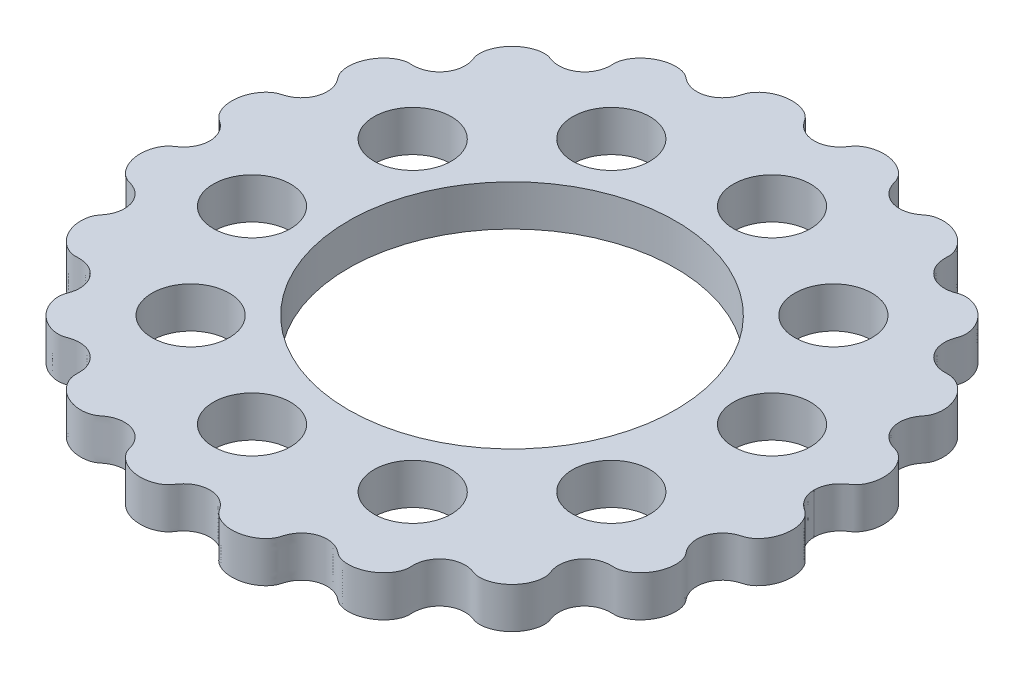
SolidWorks part; units mm, degrees
ref_plane "Front Plane" through (0, 0, 0) normal (0, 0, 1) x (1, 0, 0)
ref_plane "Top Plane" through (0, 0, 0) normal (0, 1, 0) x (1, 0, 0)
ref_plane "Right Plane" through (0, 0, 0) normal (1, 0, 0) x (0, 0, -1)
sketch "Sketch1" plane through (0, 0, 0) normal (0, 1, 0) x (1, 0, 0)
  line L0 (-115.1642, 0) -> (115.1642, 0) construction
  line L1 (0, 0) -> (71.6074, 11.3415)
  line L2 (0, 0) -> (49.3844, 7.8217)
  circle A0 centre (0, 0) radius 36
  circle A11 centre (49.3844, 7.8217) radius 8.5
  circle A12 centre (44.5503, -22.6995) radius 8.5
  circle A13 centre (22.6995, -44.5503) radius 8.5
  circle A14 centre (-7.8217, -49.3844) radius 8.5
  circle A15 centre (-35.3553, -35.3553) radius 8.5
  circle A16 centre (-49.3844, -7.8217) radius 8.5
  circle A17 centre (-44.5503, 22.6995) radius 8.5
  circle A18 centre (-22.6995, 44.5503) radius 8.5
  circle A19 centre (7.8217, 49.3844) radius 8.5
  circle A20 centre (35.3553, 35.3553) radius 8.5
  spline S0 degree 4 poles (65.4605, 29.5127) (65.4655, 29.1686) (65.4411, 28.6953) (65.3529, 28.0968) (65.1422, 27.3959) (64.9669, 26.9794) (64.7793, 26.6408) (64.5721, 26.3406) (64.3602, 26.0705) (64.1267, 25.7629) (63.886, 25.4071) (63.6576, 25.018) (63.4493, 24.5932) (63.2212, 24.0118) (63.0252, 23.2599) (62.9311, 22.3562) (63.0135, 21.3212) (63.2874, 20.3043) (63.7526, 19.3426) (64.4013, 18.4733) (65.1379, 17.8054) (65.8842, 17.3263) (66.5245, 17.0291) (66.9742, 16.8668) (67.3149, 16.7623) (67.5855, 16.6832) (67.8556, 16.6018) (68.139, 16.4927) (68.4292, 16.347) (68.7442, 16.1592) (69.1239, 15.8899) (69.5685, 15.5009) (70.0111, 15.0131) (70.4008, 14.4816) (70.6777, 14.0268) (70.8691, 13.6636) (70.9988, 13.3869) (71.0782, 13.2046) (71.1589, 13.0042) (71.23, 12.8148) (71.2726, 12.6939) (71.3209, 12.5457) (71.3774, 12.3645) (71.4665, 12.0546) (71.5573, 11.6609) (71.6461, 11.1378) (71.6973, 10.5855) (71.7141, 10.0755) (71.6934, 9.4422) (71.604, 8.684) (71.4252, 7.9197) (71.1461, 7.1625) (70.8392, 6.5565) (70.5425, 6.0894) (70.2317, 5.6994) (69.9193, 5.3829) (69.5974, 5.1276) (69.2839, 4.9185) (68.9179, 4.6631) (68.5115, 4.3444) (68.0178, 3.8822) (67.479, 3.228) (67.0049, 2.4212) (66.6487, 1.4477) (66.4722, 0.3979) (66.4959, -0.6726) (66.728, -1.7332) (67.1223, -2.6449) (67.6013, -3.3859) (68.0735, -3.9308) (68.4846, -4.3184) (68.8764, -4.6317) (69.2337, -4.8858) (69.5643, -5.1036) (69.8432, -5.3215) (70.1179, -5.5817) (70.4008, -5.9017) (70.7023, -6.3238) (71.0546, -6.9527) (71.3757, -7.7472) (71.6154, -8.6857) (71.7312, -9.759) (71.7014, -10.8232) (71.5361, -11.8601) (71.2442, -12.8535) (70.8335, -13.7883) (70.3588, -14.5657) (69.8607, -15.1916) (69.3853, -15.6662) (68.9647, -16.0122) (68.5481, -16.287) (68.1887, -16.4718) (67.8853, -16.5895) (67.6027, -16.679) (67.3177, -16.7605) (66.9147, -16.8851) (66.4027, -17.0799) (65.771, -17.3914) (65.047, -17.8802) (64.3539, -18.5333) (63.7378, -19.3727) (63.275, -20.3353) (63.0008, -21.3699) (62.9289, -22.4535) (63.0528, -23.4279) (63.2978, -24.2511) (63.587, -24.8932) (63.8609, -25.3718) (64.1452, -25.79) (64.4255, -26.1537) (64.7197, -26.5327) (64.9654, -26.9687) (65.1645, -27.4552) (65.3153, -27.9862) (65.4369, -28.6607) (65.4867, -29.4797) (65.4211, -30.426) (65.1959, -31.4778) (64.8335, -32.4836) (64.3459, -33.4278) (63.7436, -34.2955) (63.0364, -35.0719) (62.3194, -35.6676) (61.6326, -36.1029) (61.0186, -36.3975) (60.5014, -36.5851) (60.0027, -36.7056) (59.5828, -36.7546) (59.2387, -36.7552) (58.9195, -36.7455) (58.6002, -36.738) (58.1866, -36.7449) (57.6806, -36.7888) (57.0258, -36.9034) (56.2311, -37.1486) (55.3802, -37.5682) (54.5248, -38.2129) (53.7989, -39.0162) (53.2457, -39.9314) (52.8764, -40.9322) (52.7129, -41.9038) (52.7111, -42.801) (52.8153, -43.5274) (52.9414, -44.0332) (53.0556, -44.396) (53.1493, -44.6684) (53.2479, -44.939) (53.365, -45.2914) (53.4522, -45.7377) (53.492, -46.2577) (53.4686, -46.8459) (53.3634, -47.5564) (53.1367, -48.3745) (52.7684, -49.2465) (52.2349, -50.1437) (51.5838, -50.9705) (50.825, -51.7126) (49.9786, -52.3468) (49.0582, -52.8607) (48.2008, -53.1936) (47.4397, -53.384) (46.7836, -53.4712) (46.2434, -53.4905) (45.7356, -53.453) (45.3175, -53.3699) (44.9917, -53.2655) (44.6996, -53.161) (44.407, -53.0576) (44.0063, -52.933) (43.491, -52.8115) (42.8001, -52.7145) (41.9272, -52.71) (40.953, -52.8675) (39.9202, -53.2489) (38.9741, -53.8277) (38.1691, -54.5703) (37.5299, -55.4429) (37.1019, -56.344) (36.8793, -57.1248) (36.7803, -57.7595) (36.7454, -58.2289) (36.7381, -58.5957) (36.7456, -58.9543) (36.7588, -59.3048) (36.7453, -59.7001) (36.6779, -60.1352) (36.5493, -60.6146) (36.3491, -61.1297) (36.0405, -61.7408) (35.5897, -62.4233) (34.9769, -63.1346) (34.1812, -63.8335) (33.2956, -64.4242) (32.3354, -64.8968) (31.316, -65.2408) (30.2533, -65.4441) (29.3028, -65.4867) (28.4861, -65.415) (27.8172, -65.2736) (27.3586, -65.1269) (26.9828, -64.9645) (26.6415, -64.7795) (26.3825, -64.6044) (26.1435, -64.417) (25.8617, -64.202) (25.5735, -63.9954) (25.2136, -63.7661) (24.7736, -63.5314) (24.1733, -63.2738) (23.3906, -63.046) (22.4364, -62.9272) (21.3345, -63.0057) (20.2693, -63.297) (19.3028, -63.7777) (18.4651, -64.4155) (17.8212, -65.1237) (17.3489, -65.8446) (17.0492, -66.4737) (16.8796, -66.9362) (16.7731, -67.2787) (16.697, -67.538) (16.6206, -67.7971) (16.4999, -68.13) (16.3026, -68.5209) (16.0236, -68.9517) (15.6499, -69.4069) (15.1392, -69.9099) (14.4692, -70.4259) (13.6607, -70.8988) (12.7127, -71.2944) (11.702, -71.5708) (10.6433, -71.7174) (9.5744, -71.7223) (8.5152, -71.5812) (7.6197, -71.3301) (6.8918, -71.0218) (6.3681, -70.7238) (6.0257, -70.4887) (5.7564, -70.2722) (5.5526, -70.086) (5.3293, -69.8531) (5.1014, -69.5624) (4.8738, -69.215) (4.6046, -68.8398) (4.2946, -68.4584) (3.9347, -68.0813) (3.4174, -67.6285) (2.7042, -67.1529) (1.7921, -66.7433) (0.6851, -66.4941) (-0.4667, -66.4704) (-1.4606, -66.6552) (-2.2728, -66.9558) (-2.9107, -67.2974) (-3.3788, -67.6111) (-3.7983, -67.9554) (-4.1704, -68.3213) (-4.4603, -68.6577) (-4.6823, -68.9486) (-4.8581, -69.1976) (-4.9952, -69.3993) (-5.1396, -69.6076) (-5.3007, -69.8157) (-5.4839, -70.0179) (-5.6881, -70.2127) (-5.9591, -70.4393) (-6.3053, -70.6848) (-6.8327, -70.9933) (-7.5648, -71.3113) (-8.469, -71.5723) (-9.5418, -71.7212) (-10.6244, -71.7198) (-11.6959, -71.5725) (-12.7127, -71.2944) (-13.6607, -70.8988) (-14.4692, -70.4259) (-15.1392, -69.9099) (-15.6499, -69.4069) (-16.0236, -68.9517) (-16.3026, -68.5209) (-16.4999, -68.13) (-16.6206, -67.7971) (-16.697, -67.538) (-16.7731, -67.2787) (-16.8796, -66.9362) (-17.0492, -66.4737) (-17.3489, -65.8446) (-17.8212, -65.1237) (-18.4651, -64.4155) (-19.3028, -63.7777) (-20.2693, -63.297) (-21.3345, -63.0057) (-22.4364, -62.9272) (-23.3906, -63.046) (-24.1733, -63.2738) (-24.7736, -63.5314) (-25.2137, -63.7661) (-25.5735, -63.9954) (-25.8617, -64.202) (-26.0964, -64.3813) (-26.2831, -64.5262) (-26.4805, -64.6709) (-26.6936, -64.8076) (-26.9828, -64.9646) (-27.3587, -65.1269) (-27.8172, -65.2736) (-28.4861, -65.415) (-29.3028, -65.4868) (-30.2533, -65.4441) (-31.316, -65.2408) (-32.3354, -64.8968) (-33.2956, -64.4242) (-34.1812, -63.8335) (-34.9769, -63.1346) (-35.5897, -62.4233) (-36.0405, -61.7408) (-36.3491, -61.1297) (-36.5493, -60.6146) (-36.6779, -60.1352) (-36.7453, -59.7001) (-36.7588, -59.3048) (-36.7456, -58.9543) (-36.7381, -58.5957) (-36.7454, -58.2289) (-36.7803, -57.7595) (-36.8793, -57.1248) (-37.1019, -56.344) (-37.5299, -55.4429) (-38.1691, -54.5703) (-38.9741, -53.8277) (-39.9202, -53.2489) (-40.953, -52.8675) (-41.9272, -52.71) (-42.8001, -52.7145) (-43.491, -52.8115) (-44.0063, -52.933) (-44.407, -53.0576) (-44.6996, -53.161) (-44.9917, -53.2655) (-45.3175, -53.3699) (-45.7356, -53.453) (-46.2434, -53.4905) (-46.7836, -53.4712) (-47.4397, -53.384) (-48.2008, -53.1936) (-49.0582, -52.8607) (-49.9786, -52.3468) (-50.825, -51.7126) (-51.5838, -50.9705) (-52.2349, -50.1437) (-52.7684, -49.2465) (-53.1367, -48.3745) (-53.3634, -47.5564) (-53.4686, -46.8459) (-53.492, -46.2577) (-53.4522, -45.7377) (-53.365, -45.2914) (-53.2479, -44.939) (-53.1493, -44.6684) (-53.0556, -44.396) (-52.9697, -44.1229) (-52.8837, -43.8018) (-52.7883, -43.3387) (-52.7113, -42.7066) (-52.7129, -41.9038) (-52.8764, -40.9322) (-53.2457, -39.9314) (-53.7989, -39.0162) (-54.5248, -38.2129) (-55.3802, -37.5682) (-56.2311, -37.1486) (-57.0258, -36.9034) (-57.6806, -36.7888) (-58.1866, -36.7449) (-58.6002, -36.738) (-58.9195, -36.7455) (-59.2387, -36.7552) (-59.5828, -36.7546) (-60.0027, -36.7056) (-60.5014, -36.5851) (-61.0186, -36.3975) (-61.6326, -36.1029) (-62.3194, -35.6676) (-63.0364, -35.0719) (-63.7436, -34.2955) (-64.3459, -33.4278) (-64.8335, -32.4836) (-65.1959, -31.4778) (-65.4211, -30.426) (-65.4867, -29.4797) (-65.4369, -28.6607) (-65.3153, -27.9862) (-65.1645, -27.4552) (-64.9654, -26.9687) (-64.7197, -26.5327) (-64.4255, -26.1537) (-64.1452, -25.79) (-63.8609, -25.3718) (-63.587, -24.8932) (-63.2978, -24.2511) (-63.0528, -23.4279) (-62.9289, -22.4535) (-63.0008, -21.3699) (-63.275, -20.3353) (-63.7378, -19.3727) (-64.3539, -18.5333) (-65.047, -17.8802) (-65.771, -17.3914) (-66.4027, -17.0799) (-66.9147, -16.8851) (-67.3177, -16.7605) (-67.6027, -16.679) (-67.8853, -16.5895) (-68.1887, -16.4718) (-68.5481, -16.287) (-68.9647, -16.0122) (-69.3853, -15.6662) (-69.8607, -15.1916) (-70.3588, -14.5657) (-70.8335, -13.7883) (-71.2442, -12.8535) (-71.5361, -11.8601) (-71.7014, -10.8232) (-71.7312, -9.759) (-71.6154, -8.6857) (-71.3757, -7.7472) (-71.0546, -6.9527) (-70.7023, -6.3238) (-70.4008, -5.9017) (-70.1179, -5.5817) (-69.8432, -5.3215) (-69.5643, -5.1036) (-69.2337, -4.8858) (-68.8764, -4.6317) (-68.4846, -4.3184) (-68.0735, -3.9308) (-67.6013, -3.3859) (-67.1223, -2.6449) (-66.728, -1.7332) (-66.4959, -0.6726) (-66.4722, 0.3979) (-66.6487, 1.4477) (-67.0049, 2.4212) (-67.479, 3.228) (-68.0178, 3.8822) (-68.5115, 4.3445) (-68.9179, 4.6631) (-69.2839, 4.9185) (-69.5974, 5.1275) (-69.9193, 5.3829) (-70.2317, 5.6994) (-70.5425, 6.0895) (-70.8393, 6.5564) (-71.1461, 7.1627) (-71.4254, 7.9193) (-71.6038, 8.6846) (-71.6937, 9.4414) (-71.7137, 10.0768) (-71.6982, 10.5829) (-71.6528, 11.0541) (-71.5898, 11.476) (-71.5079, 11.8717) (-71.4425, 12.139) (-71.3774, 12.3645) (-71.3208, 12.546) (-71.2727, 12.6938) (-71.23, 12.8149) (-71.1589, 13.0042) (-71.0782, 13.2046) (-70.9988, 13.3869) (-70.8691, 13.6636) (-70.6777, 14.0268) (-70.4008, 14.4816) (-70.0111, 15.0131) (-69.5685, 15.5009) (-69.1239, 15.8899) (-68.7442, 16.1592) (-68.4292, 16.347) (-68.139, 16.4927) (-67.8556, 16.6018) (-67.5855, 16.6832) (-67.3149, 16.7623) (-66.9742, 16.8668) (-66.5245, 17.0291) (-65.8842, 17.3263) (-65.1379, 17.8054) (-64.4013, 18.4733) (-63.7491, 19.3473) (-63.28, 20.3205) (-63.0059, 21.3554) (-62.9309, 22.4063) (-63.0352, 23.3171) (-63.2396, 24.0678) (-63.4711, 24.642) (-63.6812, 25.0611) (-63.9101, 25.4449) (-64.1204, 25.7515) (-64.3116, 26.0062) (-64.4807, 26.2243) (-64.6214, 26.4108) (-64.7943, 26.6657) (-64.9775, 27.0024) (-65.1491, 27.4157) (-65.3551, 28.1105) (-65.4416, 28.7032) (-65.4654, 29.172) (-65.4605, 29.5127) knots 0 0 0 0 0 0.004123 0.005669 0.007215 0.008756 0.009527 0.010298 0.011583 0.012869 0.014155 0.015441 0.016987 0.018533 0.02163 0.024723 0.027815 0.030907 0.034179 0.03745 0.040732 0.042749 0.044767 0.045893 0.046456 0.04702 0.048146 0.049273 0.050089 0.050906 0.052538 0.054845 0.057151 0.058784 0.060416 0.061233 0.062049 0.062457 0.062865 0.063682 0.064216 0.064483 0.06475 0.065818 0.067955 0.069475 0.070996 0.072517 0.074037 0.077079 0.08012 0.0819 0.08368 0.085209 0.086738 0.087867 0.088995 0.090124 0.091252 0.093215 0.095179 0.098214 0.101374 0.104369 0.107533 0.1109 0.114125 0.117298 0.119365 0.121433 0.122746 0.124059 0.125372 0.126686 0.12749 0.128294 0.129902 0.131797 0.133692 0.136915 0.140139 0.143363 0.146587 0.149637 0.152687 0.155738 0.158788 0.160518 0.162248 0.163776 0.165304 0.166488 0.16708 0.167672 0.168855 0.170039 0.172134 0.174229 0.177278 0.18047 0.183483 0.186637 0.190007 0.193215 0.196415 0.198338 0.200262 0.201638 0.203015 0.204391 0.205768 0.207378 0.208989 0.210679 0.212369 0.215581 0.218794 0.222006 0.225218 0.228355 0.231492 0.234629 0.237765 0.239488 0.24121 0.242778 0.244347 0.245622 0.24626 0.246898 0.248174 0.24945 0.251214 0.252979 0.256128 0.259382 0.262517 0.265738 0.269027 0.272117 0.275225 0.277481 0.279736 0.280887 0.281463 0.282038 0.283189 0.28434 0.285906 0.287472 0.289426 0.29138 0.294497 0.297615 0.300733 0.30385 0.307074 0.310298 0.313371 0.316443 0.31806 0.319676 0.321293 0.322909 0.324149 0.324768 0.325388 0.326627 0.327867 0.329796 0.331725 0.334972 0.338289 0.341548 0.344836 0.34818 0.35133 0.354431 0.356724 0.35787 0.359017 0.360068 0.361118 0.362169 0.36322 0.3648 0.366381 0.368106 0.36983 0.372993 0.376156 0.379319 0.382483 0.385713 0.388944 0.392175 0.395406 0.397073 0.39874 0.400356 0.401164 0.401972 0.403388 0.404096 0.404804 0.40622 0.407635 0.409205 0.410774 0.414037 0.417372 0.420655 0.423928 0.427187 0.430227 0.4332 0.43534 0.437479 0.438558 0.439098 0.439638 0.440717 0.441796 0.443334 0.444872 0.446856 0.44884 0.451909 0.454977 0.458046 0.461115 0.464432 0.467749 0.470814 0.47388 0.475539 0.477198 0.478024 0.478851 0.479677 0.480504 0.481887 0.48327 0.484653 0.486036 0.487772 0.489508 0.492878 0.49627 0.499675 0.503014 0.506592 0.508301 0.51001 0.511672 0.513334 0.514795 0.516256 0.516987 0.517718 0.518448 0.519179 0.520024 0.520869 0.521714 0.522559 0.524254 0.525949 0.529024 0.532099 0.535492 0.538885 0.541954 0.545023 0.548091 0.55116 0.553144 0.555128 0.556666 0.558204 0.559283 0.560362 0.560902 0.561442 0.562521 0.56466 0.5668 0.569773 0.572812 0.576072 0.579345 0.582628 0.585963 0.589226 0.590795 0.592365 0.59378 0.595196 0.595904 0.596612 0.59732 0.598028 0.598836 0.599644 0.60126 0.602927 0.604594 0.607825 0.611056 0.614287 0.617517 0.620681 0.623844 0.627007 0.63017 0.631894 0.633619 0.635199 0.63678 0.637831 0.638882 0.639932 0.640983 0.64213 0.643276 0.645569 0.64867 0.65182 0.655164 0.658452 0.661711 0.665028 0.668275 0.670204 0.672133 0.673372 0.674612 0.675232 0.675851 0.677091 0.678707 0.680324 0.68194 0.683557 0.686629 0.689702 0.692926 0.69615 0.699267 0.702385 0.705503 0.70862 0.710574 0.712528 0.714094 0.71566 0.716811 0.717962 0.718537 0.719113 0.720264 0.721391 0.722519 0.724775 0.727883 0.730973 0.734262 0.737483 0.740618 0.743872 0.747021 0.748786 0.75055 0.751826 0.753102 0.75374 0.754378 0.755653 0.757222 0.75879 0.760512 0.762234 0.765371 0.768508 0.771645 0.774782 0.777994 0.781206 0.784419 0.787631 0.789321 0.791011 0.792622 0.794232 0.795609 0.796985 0.798362 0.799738 0.801662 0.803585 0.806785 0.809993 0.813363 0.816517 0.81953 0.822722 0.825771 0.827866 0.829961 0.831145 0.832328 0.83292 0.833512 0.834696 0.836224 0.837752 0.839482 0.841212 0.844262 0.847313 0.850363 0.853413 0.856637 0.859861 0.863084 0.866308 0.868203 0.870098 0.871706 0.87251 0.873314 0.874628 0.875941 0.877254 0.878567 0.880635 0.882702 0.885875 0.8891 0.892467 0.895631 0.898626 0.901786 0.904821 0.906785 0.908748 0.909876 0.911005 0.912133 0.913262 0.914791 0.91632 0.9181 0.91988 0.922921 0.925963 0.927483 0.929004 0.930525 0.932045 0.933114 0.934182 0.93525 0.935517 0.935784 0.936318 0.937135 0.937543 0.937951 0.938767 0.939584 0.941216 0.942849 0.945155 0.947462 0.949094 0.949911 0.950727 0.951854 0.95298 0.953544 0.954107 0.955233 0.957251 0.959268 0.96255 0.965821 0.969093 0.972255 0.975418 0.978575 0.981646 0.98318 0.984714 0.985986 0.987258 0.98853 0.989166 0.989802 0.990566 0.991329 0.992855 0.994386 0.995917 1 1 1 1 1 construction
  spline S1 degree 4 poles (66.5, 0) (66.5, -0.3064) (66.5419, -0.882) (66.7179, -1.7097) (67.1223, -2.6449) (67.6013, -3.3859) (68.0735, -3.9308) (68.4846, -4.3184) (68.8764, -4.6317) (69.2337, -4.8858) (69.5643, -5.1036) (69.8432, -5.3215) (70.1179, -5.5817) (70.4008, -5.9017) (70.7023, -6.3238) (71.0546, -6.9527) (71.3757, -7.7472) (71.6154, -8.6857) (71.7312, -9.759) (71.7014, -10.8232) (71.5361, -11.8601) (71.2442, -12.8535) (70.8335, -13.7883) (70.3588, -14.5657) (69.8607, -15.1916) (69.3853, -15.6662) (68.9647, -16.0122) (68.5481, -16.287) (68.1887, -16.4718) (67.8853, -16.5895) (67.6027, -16.679) (67.3177, -16.7605) (66.9147, -16.8851) (66.4027, -17.0799) (65.771, -17.3914) (65.047, -17.8802) (64.3539, -18.5333) (63.7378, -19.3727) (63.275, -20.3353) (63.0008, -21.3699) (62.9289, -22.4535) (63.0528, -23.4279) (63.2978, -24.2511) (63.587, -24.8932) (63.8609, -25.3718) (64.1452, -25.79) (64.4255, -26.1537) (64.7197, -26.5327) (64.9654, -26.9687) (65.1645, -27.4552) (65.3153, -27.9862) (65.4369, -28.6607) (65.4867, -29.4797) (65.4211, -30.426) (65.1959, -31.4778) (64.8335, -32.4836) (64.3459, -33.4278) (63.7436, -34.2955) (63.0364, -35.0719) (62.3194, -35.6676) (61.6326, -36.1029) (61.0186, -36.3975) (60.5014, -36.5851) (60.0027, -36.7056) (59.5828, -36.7546) (59.2387, -36.7552) (58.9195, -36.7455) (58.6002, -36.738) (58.1866, -36.7449) (57.6806, -36.7888) (57.0258, -36.9034) (56.2311, -37.1486) (55.3802, -37.5682) (54.5248, -38.2129) (53.7989, -39.0162) (53.2457, -39.9314) (52.8764, -40.9322) (52.7129, -41.9038) (52.7111, -42.801) (52.8153, -43.5274) (52.9414, -44.0332) (53.0556, -44.396) (53.1493, -44.6684) (53.2479, -44.939) (53.365, -45.2914) (53.4522, -45.7377) (53.492, -46.2577) (53.4686, -46.8459) (53.3634, -47.5564) (53.1367, -48.3745) (52.7684, -49.2465) (52.2349, -50.1437) (51.5838, -50.9705) (50.825, -51.7126) (49.9786, -52.3468) (49.0582, -52.8607) (48.2008, -53.1936) (47.4397, -53.384) (46.7836, -53.4712) (46.2434, -53.4905) (45.7356, -53.453) (45.3175, -53.3699) (44.9917, -53.2655) (44.6996, -53.161) (44.407, -53.0576) (44.0063, -52.933) (43.491, -52.8115) (42.8001, -52.7145) (41.9272, -52.71) (40.953, -52.8675) (39.9202, -53.2489) (38.9741, -53.8277) (38.1691, -54.5703) (37.5299, -55.4429) (37.1019, -56.344) (36.8793, -57.1248) (36.7803, -57.7595) (36.7454, -58.2289) (36.7381, -58.5957) (36.7456, -58.9543) (36.7588, -59.3048) (36.7453, -59.7001) (36.6779, -60.1352) (36.5493, -60.6146) (36.3491, -61.1297) (36.0405, -61.7408) (35.5897, -62.4233) (34.9769, -63.1346) (34.1812, -63.8335) (33.2956, -64.4242) (32.3354, -64.8968) (31.316, -65.2408) (30.2533, -65.4441) (29.3028, -65.4867) (28.4861, -65.415) (27.8172, -65.2736) (27.3586, -65.1269) (26.9828, -64.9645) (26.6415, -64.7795) (26.3825, -64.6044) (26.1435, -64.417) (25.8617, -64.202) (25.5735, -63.9954) (25.2136, -63.7661) (24.7736, -63.5314) (24.1733, -63.2738) (23.3906, -63.046) (22.4364, -62.9272) (21.3345, -63.0057) (20.2693, -63.297) (19.3028, -63.7777) (18.4651, -64.4155) (17.8212, -65.1237) (17.3489, -65.8446) (17.0492, -66.4737) (16.8796, -66.9362) (16.7731, -67.2787) (16.697, -67.538) (16.6206, -67.7971) (16.4999, -68.13) (16.3026, -68.5209) (16.0236, -68.9517) (15.6499, -69.4069) (15.1392, -69.9099) (14.4692, -70.4259) (13.6607, -70.8988) (12.7127, -71.2944) (11.702, -71.5708) (10.6433, -71.7174) (9.5744, -71.7223) (8.5152, -71.5812) (7.6197, -71.3301) (6.8918, -71.0218) (6.3681, -70.7238) (6.0257, -70.4887) (5.7564, -70.2722) (5.5526, -70.086) (5.3293, -69.8531) (5.1014, -69.5624) (4.8738, -69.215) (4.6046, -68.8398) (4.2946, -68.4584) (3.9347, -68.0813) (3.4174, -67.6285) (2.7042, -67.1529) (1.7921, -66.7433) (0.6851, -66.4941) (-0.4667, -66.4704) (-1.4606, -66.6552) (-2.2728, -66.9558) (-2.9107, -67.2974) (-3.3788, -67.6111) (-3.7983, -67.9554) (-4.1704, -68.3213) (-4.4603, -68.6577) (-4.6823, -68.9486) (-4.8581, -69.1976) (-4.9952, -69.3993) (-5.1396, -69.6076) (-5.3007, -69.8157) (-5.4839, -70.0179) (-5.6881, -70.2127) (-5.9591, -70.4393) (-6.3053, -70.6848) (-6.8327, -70.9933) (-7.5648, -71.3113) (-8.469, -71.5723) (-9.5418, -71.7212) (-10.6244, -71.7198) (-11.6959, -71.5725) (-12.7127, -71.2944) (-13.6607, -70.8988) (-14.4692, -70.4259) (-15.1392, -69.9099) (-15.6499, -69.4069) (-16.0236, -68.9517) (-16.3026, -68.5209) (-16.4999, -68.13) (-16.6206, -67.7971) (-16.697, -67.538) (-16.7731, -67.2787) (-16.8796, -66.9362) (-17.0492, -66.4737) (-17.3489, -65.8446) (-17.8212, -65.1237) (-18.4651, -64.4155) (-19.3028, -63.7777) (-20.2693, -63.297) (-21.3345, -63.0057) (-22.4364, -62.9272) (-23.3906, -63.046) (-24.1733, -63.2738) (-24.7736, -63.5314) (-25.2137, -63.7661) (-25.5735, -63.9954) (-25.8617, -64.202) (-26.0964, -64.3813) (-26.2831, -64.5262) (-26.4805, -64.6709) (-26.6936, -64.8076) (-26.9828, -64.9646) (-27.3587, -65.1269) (-27.8172, -65.2736) (-28.4861, -65.415) (-29.3028, -65.4868) (-30.2533, -65.4441) (-31.316, -65.2408) (-32.3354, -64.8968) (-33.2956, -64.4242) (-34.1812, -63.8335) (-34.9769, -63.1346) (-35.5897, -62.4233) (-36.0405, -61.7408) (-36.3491, -61.1297) (-36.5493, -60.6146) (-36.6779, -60.1352) (-36.7453, -59.7001) (-36.7588, -59.3048) (-36.7456, -58.9543) (-36.7381, -58.5957) (-36.7454, -58.2289) (-36.7803, -57.7595) (-36.8793, -57.1248) (-37.1019, -56.344) (-37.5299, -55.4429) (-38.1691, -54.5703) (-38.9741, -53.8277) (-39.9202, -53.2489) (-40.953, -52.8675) (-41.9272, -52.71) (-42.8001, -52.7145) (-43.491, -52.8115) (-44.0063, -52.933) (-44.407, -53.0576) (-44.6996, -53.161) (-44.9917, -53.2655) (-45.3175, -53.3699) (-45.7356, -53.453) (-46.2434, -53.4905) (-46.7836, -53.4712) (-47.4397, -53.384) (-48.2008, -53.1936) (-49.0582, -52.8607) (-49.9786, -52.3468) (-50.825, -51.7126) (-51.5838, -50.9705) (-52.2349, -50.1437) (-52.7684, -49.2465) (-53.1367, -48.3745) (-53.3634, -47.5564) (-53.4686, -46.8459) (-53.492, -46.2577) (-53.4522, -45.7377) (-53.365, -45.2914) (-53.2479, -44.939) (-53.1493, -44.6684) (-53.0556, -44.396) (-52.9697, -44.1229) (-52.8837, -43.8018) (-52.7883, -43.3387) (-52.7113, -42.7066) (-52.7129, -41.9038) (-52.8764, -40.9322) (-53.2457, -39.9314) (-53.7989, -39.0162) (-54.5248, -38.2129) (-55.3802, -37.5682) (-56.2311, -37.1486) (-57.0258, -36.9034) (-57.6806, -36.7888) (-58.1866, -36.7449) (-58.6002, -36.738) (-58.9195, -36.7455) (-59.2387, -36.7552) (-59.5828, -36.7546) (-60.0027, -36.7056) (-60.5014, -36.5851) (-61.0186, -36.3975) (-61.6326, -36.1029) (-62.3194, -35.6676) (-63.0364, -35.0719) (-63.7436, -34.2955) (-64.3459, -33.4278) (-64.8335, -32.4836) (-65.1959, -31.4778) (-65.4211, -30.426) (-65.4867, -29.4797) (-65.4369, -28.6607) (-65.3153, -27.9862) (-65.1645, -27.4552) (-64.9654, -26.9687) (-64.7197, -26.5327) (-64.4255, -26.1537) (-64.1452, -25.79) (-63.8609, -25.3718) (-63.587, -24.8932) (-63.2978, -24.2511) (-63.0528, -23.4279) (-62.9289, -22.4535) (-63.0008, -21.3699) (-63.275, -20.3353) (-63.7378, -19.3727) (-64.3539, -18.5333) (-65.047, -17.8802) (-65.771, -17.3914) (-66.4027, -17.0799) (-66.9147, -16.8851) (-67.3177, -16.7605) (-67.6027, -16.679) (-67.8853, -16.5895) (-68.1887, -16.4718) (-68.5481, -16.287) (-68.9647, -16.0122) (-69.3853, -15.6662) (-69.8607, -15.1916) (-70.3588, -14.5657) (-70.8335, -13.7883) (-71.2442, -12.8535) (-71.5361, -11.8601) (-71.7014, -10.8232) (-71.7312, -9.759) (-71.6154, -8.6857) (-71.3757, -7.7472) (-71.0546, -6.9527) (-70.7023, -6.3238) (-70.4008, -5.9017) (-70.1179, -5.5817) (-69.8432, -5.3215) (-69.5643, -5.1036) (-69.2337, -4.8858) (-68.8764, -4.6317) (-68.4846, -4.3184) (-68.0735, -3.9308) (-67.6013, -3.3859) (-67.1223, -2.6449) (-66.7179, -1.7097) (-66.5419, -0.882) (-66.5, -0.3064) (-66.5, 0) knots 0.107228 0.107228 0.107228 0.107228 0.107228 0.1109 0.114125 0.117298 0.119365 0.121433 0.122746 0.124059 0.125372 0.126686 0.12749 0.128294 0.129902 0.131797 0.133692 0.136915 0.140139 0.143363 0.146587 0.149637 0.152687 0.155738 0.158788 0.160518 0.162248 0.163776 0.165304 0.166488 0.16708 0.167672 0.168855 0.170039 0.172134 0.174229 0.177278 0.18047 0.183483 0.186637 0.190007 0.193215 0.196415 0.198338 0.200262 0.201638 0.203015 0.204391 0.205768 0.207378 0.208989 0.210679 0.212369 0.215581 0.218794 0.222006 0.225218 0.228355 0.231492 0.234629 0.237765 0.239488 0.24121 0.242778 0.244347 0.245622 0.24626 0.246898 0.248174 0.24945 0.251214 0.252979 0.256128 0.259382 0.262517 0.265738 0.269027 0.272117 0.275225 0.277481 0.279736 0.280887 0.281463 0.282038 0.283189 0.28434 0.285906 0.287472 0.289426 0.29138 0.294497 0.297615 0.300733 0.30385 0.307074 0.310298 0.313371 0.316443 0.31806 0.319676 0.321293 0.322909 0.324149 0.324768 0.325388 0.326627 0.327867 0.329796 0.331725 0.334972 0.338289 0.341548 0.344836 0.34818 0.35133 0.354431 0.356724 0.35787 0.359017 0.360068 0.361118 0.362169 0.36322 0.3648 0.366381 0.368106 0.36983 0.372993 0.376156 0.379319 0.382483 0.385713 0.388944 0.392175 0.395406 0.397073 0.39874 0.400356 0.401164 0.401972 0.403388 0.404096 0.404804 0.40622 0.407635 0.409205 0.410774 0.414037 0.417372 0.420655 0.423928 0.427187 0.430227 0.4332 0.43534 0.437479 0.438558 0.439098 0.439638 0.440717 0.441796 0.443334 0.444872 0.446856 0.44884 0.451909 0.454977 0.458046 0.461115 0.464432 0.467749 0.470814 0.47388 0.475539 0.477198 0.478024 0.478851 0.479677 0.480504 0.481887 0.48327 0.484653 0.486036 0.487772 0.489508 0.492878 0.49627 0.499675 0.503014 0.506592 0.508301 0.51001 0.511672 0.513334 0.514795 0.516256 0.516987 0.517718 0.518448 0.519179 0.520024 0.520869 0.521714 0.522559 0.524254 0.525949 0.529024 0.532099 0.535492 0.538885 0.541954 0.545023 0.548091 0.55116 0.553144 0.555128 0.556666 0.558204 0.559283 0.560362 0.560902 0.561442 0.562521 0.56466 0.5668 0.569773 0.572812 0.576072 0.579345 0.582628 0.585963 0.589226 0.590795 0.592365 0.59378 0.595196 0.595904 0.596612 0.59732 0.598028 0.598836 0.599644 0.60126 0.602927 0.604594 0.607825 0.611056 0.614287 0.617517 0.620681 0.623844 0.627007 0.63017 0.631894 0.633619 0.635199 0.63678 0.637831 0.638882 0.639932 0.640983 0.64213 0.643276 0.645569 0.64867 0.65182 0.655164 0.658452 0.661711 0.665028 0.668275 0.670204 0.672133 0.673372 0.674612 0.675232 0.675851 0.677091 0.678707 0.680324 0.68194 0.683557 0.686629 0.689702 0.692926 0.69615 0.699267 0.702385 0.705503 0.70862 0.710574 0.712528 0.714094 0.71566 0.716811 0.717962 0.718537 0.719113 0.720264 0.721391 0.722519 0.724775 0.727883 0.730973 0.734262 0.737483 0.740618 0.743872 0.747021 0.748786 0.75055 0.751826 0.753102 0.75374 0.754378 0.755653 0.757222 0.75879 0.760512 0.762234 0.765371 0.768508 0.771645 0.774782 0.777994 0.781206 0.784419 0.787631 0.789321 0.791011 0.792622 0.794232 0.795609 0.796985 0.798362 0.799738 0.801662 0.803585 0.806785 0.809993 0.813363 0.816517 0.81953 0.822722 0.825771 0.827866 0.829961 0.831145 0.832328 0.83292 0.833512 0.834696 0.836224 0.837752 0.839482 0.841212 0.844262 0.847313 0.850363 0.853413 0.856637 0.859861 0.863084 0.866308 0.868203 0.870098 0.871706 0.87251 0.873314 0.874628 0.875941 0.877254 0.878567 0.880635 0.882702 0.885875 0.8891 0.892772 0.892772 0.892772 0.892772 0.892772
  spline S2 degree 4 poles (66.5, 0) (66.5, 0.3064) (66.5419, 0.882) (66.7179, 1.7097) (67.1223, 2.6449) (67.6013, 3.3859) (68.0735, 3.9308) (68.4846, 4.3184) (68.8764, 4.6317) (69.2337, 4.8858) (69.5643, 5.1036) (69.8432, 5.3215) (70.1179, 5.5817) (70.4008, 5.9017) (70.7023, 6.3238) (71.0546, 6.9527) (71.3757, 7.7472) (71.6154, 8.6857) (71.7312, 9.759) (71.7014, 10.8232) (71.5361, 11.8601) (71.2442, 12.8535) (70.8335, 13.7883) (70.3588, 14.5657) (69.8607, 15.1916) (69.3853, 15.6662) (68.9647, 16.0122) (68.5481, 16.287) (68.1887, 16.4718) (67.8853, 16.5895) (67.6027, 16.679) (67.3177, 16.7605) (66.9147, 16.8851) (66.4027, 17.0799) (65.771, 17.3914) (65.047, 17.8802) (64.3539, 18.5333) (63.7378, 19.3727) (63.275, 20.3353) (63.0008, 21.3699) (62.9289, 22.4535) (63.0528, 23.4279) (63.2978, 24.2511) (63.587, 24.8932) (63.8609, 25.3718) (64.1452, 25.79) (64.4255, 26.1537) (64.7197, 26.5327) (64.9654, 26.9687) (65.1645, 27.4552) (65.3153, 27.9862) (65.4369, 28.6607) (65.4867, 29.4797) (65.4211, 30.426) (65.1959, 31.4778) (64.8335, 32.4836) (64.3459, 33.4278) (63.7436, 34.2955) (63.0364, 35.0719) (62.3194, 35.6676) (61.6326, 36.1029) (61.0186, 36.3975) (60.5014, 36.5851) (60.0027, 36.7056) (59.5828, 36.7546) (59.2387, 36.7552) (58.9195, 36.7455) (58.6002, 36.738) (58.1866, 36.7449) (57.6806, 36.7888) (57.0258, 36.9034) (56.2311, 37.1486) (55.3802, 37.5682) (54.5248, 38.2129) (53.7989, 39.0162) (53.2457, 39.9314) (52.8764, 40.9322) (52.7129, 41.9038) (52.7111, 42.801) (52.8153, 43.5274) (52.9414, 44.0332) (53.0556, 44.396) (53.1493, 44.6684) (53.2479, 44.939) (53.365, 45.2914) (53.4522, 45.7377) (53.492, 46.2577) (53.4686, 46.8459) (53.3634, 47.5564) (53.1367, 48.3745) (52.7684, 49.2465) (52.2349, 50.1437) (51.5838, 50.9705) (50.825, 51.7126) (49.9786, 52.3469) (49.0582, 52.8607) (48.2008, 53.1936) (47.4397, 53.384) (46.7836, 53.4712) (46.2434, 53.4905) (45.7356, 53.453) (45.3175, 53.3699) (44.9917, 53.2655) (44.6996, 53.161) (44.407, 53.0576) (44.0063, 52.933) (43.491, 52.8115) (42.8001, 52.7145) (41.9272, 52.71) (40.953, 52.8675) (39.9202, 53.2489) (38.9741, 53.8277) (38.1691, 54.5703) (37.5299, 55.4429) (37.1019, 56.344) (36.8793, 57.1248) (36.7803, 57.7595) (36.7454, 58.2289) (36.7381, 58.5957) (36.7456, 58.9543) (36.7588, 59.3048) (36.7453, 59.7001) (36.6779, 60.1352) (36.5493, 60.6146) (36.3491, 61.1297) (36.0405, 61.7408) (35.5897, 62.4233) (34.9769, 63.1346) (34.1812, 63.8335) (33.2956, 64.4242) (32.3354, 64.8968) (31.316, 65.2408) (30.2533, 65.4441) (29.3028, 65.4867) (28.4861, 65.415) (27.8172, 65.2736) (27.3586, 65.1269) (26.9828, 64.9645) (26.6415, 64.7795) (26.3825, 64.6044) (26.1435, 64.417) (25.8617, 64.202) (25.5735, 63.9954) (25.2136, 63.7661) (24.7736, 63.5314) (24.1733, 63.2738) (23.3906, 63.046) (22.4364, 62.9272) (21.3345, 63.0057) (20.2693, 63.297) (19.3028, 63.7777) (18.4651, 64.4155) (17.8212, 65.1237) (17.3489, 65.8446) (17.0492, 66.4737) (16.8796, 66.9362) (16.7731, 67.2787) (16.697, 67.538) (16.6206, 67.7971) (16.4999, 68.13) (16.3026, 68.5209) (16.0236, 68.9517) (15.6499, 69.4069) (15.1392, 69.9099) (14.4692, 70.4259) (13.6607, 70.8988) (12.7127, 71.2944) (11.702, 71.5708) (10.6433, 71.7174) (9.5744, 71.7223) (8.5152, 71.5812) (7.6197, 71.3301) (6.8918, 71.0218) (6.3681, 70.7238) (6.0257, 70.4887) (5.7564, 70.2722) (5.5526, 70.086) (5.3293, 69.8531) (5.1014, 69.5624) (4.8738, 69.215) (4.6046, 68.8398) (4.2946, 68.4584) (3.9347, 68.0813) (3.4174, 67.6285) (2.7042, 67.1529) (1.7921, 66.7433) (0.6851, 66.4941) (-0.4667, 66.4704) (-1.4606, 66.6552) (-2.2728, 66.9558) (-2.9107, 67.2974) (-3.3788, 67.6111) (-3.7983, 67.9554) (-4.1704, 68.3213) (-4.4603, 68.6577) (-4.6823, 68.9486) (-4.8581, 69.1976) (-4.9952, 69.3993) (-5.1396, 69.6076) (-5.3007, 69.8157) (-5.4839, 70.0179) (-5.6881, 70.2127) (-5.9591, 70.4393) (-6.3053, 70.6848) (-6.8327, 70.9933) (-7.5648, 71.3113) (-8.469, 71.5723) (-9.5418, 71.7212) (-10.6244, 71.7198) (-11.6959, 71.5725) (-12.7127, 71.2944) (-13.6607, 70.8988) (-14.4692, 70.4259) (-15.1392, 69.9099) (-15.6499, 69.4069) (-16.0236, 68.9517) (-16.3026, 68.5209) (-16.4999, 68.13) (-16.6206, 67.7971) (-16.697, 67.538) (-16.7731, 67.2787) (-16.8796, 66.9362) (-17.0492, 66.4737) (-17.3489, 65.8446) (-17.8212, 65.1237) (-18.4651, 64.4155) (-19.3028, 63.7777) (-20.2693, 63.297) (-21.3345, 63.0057) (-22.4364, 62.9272) (-23.3906, 63.046) (-24.1733, 63.2738) (-24.7736, 63.5314) (-25.2137, 63.7661) (-25.5735, 63.9954) (-25.8617, 64.202) (-26.0964, 64.3813) (-26.2831, 64.5262) (-26.4805, 64.6709) (-26.6936, 64.8076) (-26.9828, 64.9646) (-27.3587, 65.1269) (-27.8172, 65.2736) (-28.4861, 65.415) (-29.3028, 65.4868) (-30.2533, 65.4441) (-31.316, 65.2408) (-32.3354, 64.8968) (-33.2956, 64.4242) (-34.1812, 63.8335) (-34.9769, 63.1346) (-35.5897, 62.4233) (-36.0405, 61.7408) (-36.3491, 61.1297) (-36.5493, 60.6146) (-36.6779, 60.1352) (-36.7453, 59.7001) (-36.7588, 59.3048) (-36.7456, 58.9543) (-36.7381, 58.5957) (-36.7454, 58.2289) (-36.7803, 57.7595) (-36.8793, 57.1248) (-37.1019, 56.344) (-37.5299, 55.4429) (-38.1691, 54.5703) (-38.9741, 53.8277) (-39.9202, 53.2489) (-40.953, 52.8675) (-41.9272, 52.71) (-42.8001, 52.7145) (-43.491, 52.8115) (-44.0063, 52.933) (-44.407, 53.0576) (-44.6996, 53.161) (-44.9917, 53.2655) (-45.3175, 53.3699) (-45.7356, 53.453) (-46.2434, 53.4905) (-46.7836, 53.4712) (-47.4397, 53.384) (-48.2008, 53.1936) (-49.0582, 52.8607) (-49.9786, 52.3469) (-50.825, 51.7126) (-51.5838, 50.9705) (-52.2349, 50.1437) (-52.7684, 49.2465) (-53.1367, 48.3745) (-53.3634, 47.5564) (-53.4686, 46.8459) (-53.492, 46.2577) (-53.4522, 45.7377) (-53.365, 45.2914) (-53.2479, 44.939) (-53.1493, 44.6684) (-53.0556, 44.396) (-52.9697, 44.1229) (-52.8837, 43.8018) (-52.7883, 43.3387) (-52.7113, 42.7066) (-52.7129, 41.9038) (-52.8764, 40.9322) (-53.2457, 39.9314) (-53.7989, 39.0162) (-54.5248, 38.2129) (-55.3802, 37.5682) (-56.2311, 37.1486) (-57.0258, 36.9034) (-57.6806, 36.7888) (-58.1866, 36.7449) (-58.6002, 36.738) (-58.9195, 36.7455) (-59.2387, 36.7552) (-59.5828, 36.7546) (-60.0027, 36.7056) (-60.5014, 36.5851) (-61.0186, 36.3975) (-61.6326, 36.1029) (-62.3194, 35.6676) (-63.0364, 35.0719) (-63.7436, 34.2955) (-64.3459, 33.4278) (-64.8335, 32.4836) (-65.1959, 31.4778) (-65.4211, 30.426) (-65.4867, 29.4797) (-65.4369, 28.6607) (-65.3153, 27.9862) (-65.1645, 27.4552) (-64.9654, 26.9687) (-64.7197, 26.5327) (-64.4255, 26.1537) (-64.1452, 25.79) (-63.8609, 25.3718) (-63.587, 24.8932) (-63.2978, 24.2511) (-63.0528, 23.4279) (-62.9289, 22.4535) (-63.0008, 21.3699) (-63.275, 20.3353) (-63.7378, 19.3727) (-64.3539, 18.5333) (-65.047, 17.8802) (-65.771, 17.3914) (-66.4027, 17.0799) (-66.9147, 16.8851) (-67.3177, 16.7605) (-67.6027, 16.679) (-67.8853, 16.5895) (-68.1887, 16.4718) (-68.5481, 16.287) (-68.9647, 16.0122) (-69.3853, 15.6662) (-69.8607, 15.1916) (-70.3588, 14.5657) (-70.8335, 13.7883) (-71.2442, 12.8535) (-71.5361, 11.8601) (-71.7014, 10.8232) (-71.7312, 9.759) (-71.6154, 8.6857) (-71.3757, 7.7472) (-71.0546, 6.9527) (-70.7023, 6.3238) (-70.4008, 5.9017) (-70.1179, 5.5817) (-69.8432, 5.3215) (-69.5643, 5.1036) (-69.2337, 4.8858) (-68.8764, 4.6317) (-68.4846, 4.3184) (-68.0735, 3.9308) (-67.6013, 3.3859) (-67.1223, 2.6449) (-66.7179, 1.7097) (-66.5419, 0.882) (-66.5, 0.3064) (-66.5, 0) knots 0.107228 0.107228 0.107228 0.107228 0.107228 0.1109 0.114125 0.117298 0.119365 0.121433 0.122746 0.124059 0.125372 0.126686 0.12749 0.128294 0.129902 0.131797 0.133692 0.136915 0.140139 0.143363 0.146587 0.149637 0.152687 0.155738 0.158788 0.160518 0.162248 0.163776 0.165304 0.166488 0.16708 0.167672 0.168855 0.170039 0.172134 0.174229 0.177278 0.18047 0.183483 0.186637 0.190007 0.193215 0.196415 0.198338 0.200262 0.201638 0.203015 0.204391 0.205768 0.207378 0.208989 0.210679 0.212369 0.215581 0.218794 0.222006 0.225218 0.228355 0.231492 0.234629 0.237765 0.239488 0.24121 0.242778 0.244347 0.245622 0.24626 0.246898 0.248174 0.24945 0.251214 0.252979 0.256128 0.259382 0.262517 0.265738 0.269027 0.272117 0.275225 0.277481 0.279736 0.280887 0.281463 0.282038 0.283189 0.28434 0.285906 0.287472 0.289426 0.29138 0.294497 0.297615 0.300733 0.30385 0.307074 0.310298 0.313371 0.316443 0.31806 0.319676 0.321293 0.322909 0.324149 0.324768 0.325388 0.326627 0.327867 0.329796 0.331725 0.334972 0.338289 0.341548 0.344836 0.34818 0.35133 0.354431 0.356724 0.35787 0.359017 0.360068 0.361118 0.362169 0.36322 0.3648 0.366381 0.368106 0.36983 0.372993 0.376156 0.379319 0.382483 0.385713 0.388944 0.392175 0.395406 0.397073 0.39874 0.400356 0.401164 0.401972 0.403388 0.404096 0.404804 0.40622 0.407635 0.409205 0.410774 0.414037 0.417372 0.420655 0.423928 0.427187 0.430227 0.4332 0.43534 0.437479 0.438558 0.439098 0.439638 0.440717 0.441796 0.443334 0.444872 0.446856 0.44884 0.451909 0.454977 0.458046 0.461115 0.464432 0.467749 0.470814 0.47388 0.475539 0.477198 0.478024 0.478851 0.479677 0.480504 0.481887 0.48327 0.484653 0.486036 0.487772 0.489508 0.492878 0.49627 0.499675 0.503014 0.506592 0.508301 0.51001 0.511672 0.513334 0.514795 0.516256 0.516987 0.517718 0.518448 0.519179 0.520024 0.520869 0.521714 0.522559 0.524254 0.525949 0.529024 0.532099 0.535492 0.538885 0.541954 0.545023 0.548091 0.55116 0.553144 0.555128 0.556666 0.558204 0.559283 0.560362 0.560902 0.561442 0.562521 0.56466 0.5668 0.569773 0.572812 0.576072 0.579345 0.582628 0.585963 0.589226 0.590795 0.592365 0.59378 0.595196 0.595904 0.596612 0.59732 0.598028 0.598836 0.599644 0.60126 0.602927 0.604594 0.607825 0.611056 0.614287 0.617517 0.620681 0.623844 0.627007 0.63017 0.631894 0.633619 0.635199 0.63678 0.637831 0.638882 0.639932 0.640983 0.64213 0.643276 0.645569 0.64867 0.65182 0.655164 0.658452 0.661711 0.665028 0.668275 0.670204 0.672133 0.673372 0.674612 0.675232 0.675851 0.677091 0.678707 0.680324 0.68194 0.683557 0.686629 0.689702 0.692926 0.69615 0.699267 0.702385 0.705503 0.70862 0.710574 0.712528 0.714094 0.71566 0.716811 0.717962 0.718537 0.719113 0.720264 0.721391 0.722519 0.724775 0.727883 0.730973 0.734262 0.737483 0.740618 0.743872 0.747021 0.748786 0.75055 0.751826 0.753102 0.75374 0.754378 0.755653 0.757222 0.75879 0.760512 0.762234 0.765371 0.768508 0.771645 0.774782 0.777994 0.781206 0.784419 0.787631 0.789321 0.791011 0.792622 0.794232 0.795609 0.796985 0.798362 0.799738 0.801662 0.803585 0.806785 0.809993 0.813363 0.816517 0.81953 0.822722 0.825771 0.827866 0.829961 0.831145 0.832328 0.83292 0.833512 0.834696 0.836224 0.837752 0.839482 0.841212 0.844262 0.847313 0.850363 0.853413 0.856637 0.859861 0.863084 0.866308 0.868203 0.870098 0.871706 0.87251 0.873314 0.874628 0.875941 0.877254 0.878567 0.880635 0.882702 0.885875 0.8891 0.892772 0.892772 0.892772 0.892772 0.892772
  point P8 (0, 0)
  point P33 (0, 0)
  point P34 (0, 0)
  dimension "D1" = 10
extrude "Boss-Extrude1" add sketch "Sketch1" along normal blind 9
